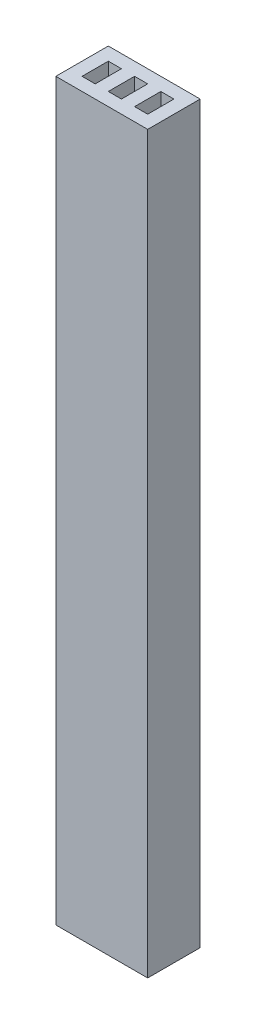
SolidWorks part; units mm, degrees
ref_plane "Front Plane" through (0, 0, 0) normal (0, 0, 1) x (1, 0, 0)
ref_plane "Top Plane" through (0, 0, 0) normal (0, 1, 0) x (1, 0, 0)
ref_plane "Right Plane" through (0, 0, 0) normal (1, 0, 0) x (0, 0, -1)
sketch "Sketch1" plane through (0, 0, 0) normal (0, 1, 0) x (1, 0, 0)
  line L0 (1, 0) -> (2, 0) construction
  line L1 (0, 0) -> (1, 0)
  line L2 (0, 0) -> (0, 2)
  line L3 (0, 2) -> (1, 2)
  line L4 (1, 0) -> (1, 2)
  line L5 (3, 0) -> (4, 0) construction
  line L6 (2, 0) -> (3, 0)
  line L7 (2, 0) -> (2, 2)
  line L8 (2, 2) -> (3, 2)
  line L9 (3, 0) -> (3, 2)
  line L10 (5, 0) -> (6, 0) construction
  line L11 (4, 0) -> (5, 0)
  line L12 (4, 0) -> (4, 2)
  line L13 (4, 2) -> (5, 2)
  line L14 (5, 0) -> (5, 2)
  line L15 (6, 0) -> (6, -1) construction
  line L16 (0, 2) -> (0, 3) construction
  line L17 (0, 3) -> (-1, 3) construction
  line L19 (-1, 3) -> (6, 3)
  line L20 (-1, 3) -> (-1, -1)
  line L21 (-1, -1) -> (6, -1)
  line L22 (6, 3) -> (6, -1)
extrude "Boss-Extrude1" add sketch "Sketch1" along normal blind 56
